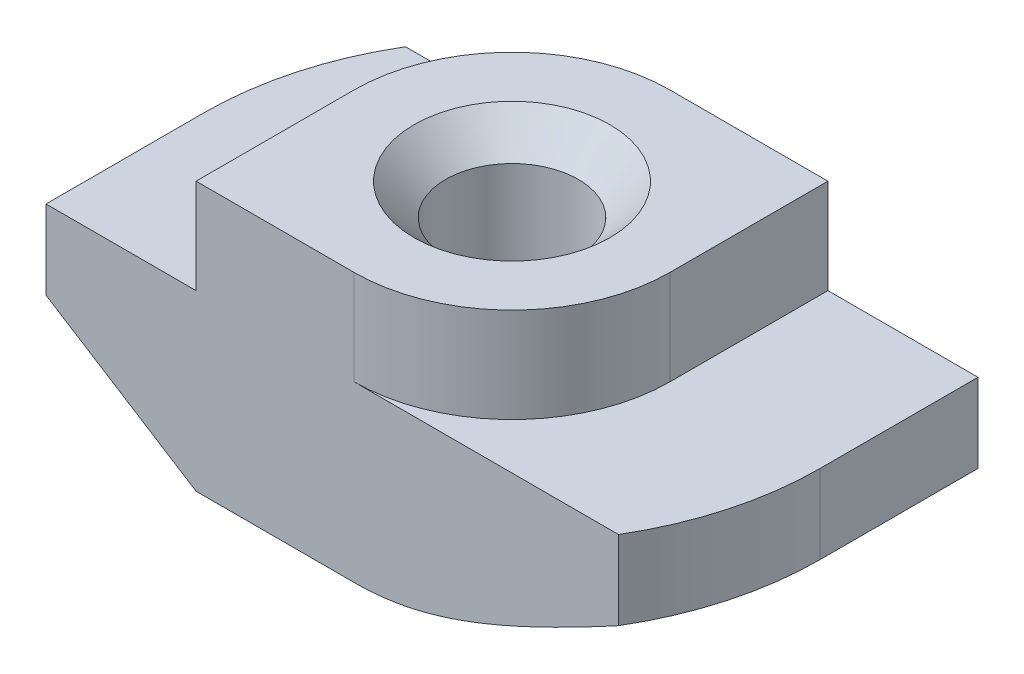
SolidWorks part; units mm, degrees
material "Сталь 20  ГОСТ 1050-2013"
ref_plane "Спереди" through (0, 0, 0) normal (0, 0, 1) x (1, 0, 0)
ref_plane "Сверху" through (0, 0, 0) normal (0, 1, 0) x (1, 0, 0)
ref_plane "Справа" through (0, 0, 0) normal (1, 0, 0) x (0, 0, -1)
sketch "Эскиз1" plane through (0, 0, 0) normal (0, 0, 1) x (1, 0, 0)
  line L0 (5, 0) -> (-5, 0)
  line L1 (-5, 0) -> (-5, -3)
  line L2 (-5, -3) -> (-9.75, -3)
  line L3 (-9.75, -3) -> (-9.75, -8.5)
  line L4 (-9.75, -8.5) -> (9.75, -8.5)
  line L5 (0, -8.5) -> (0, 0) construction
  line L6 (9.75, -3) -> (9.75, -8.5)
  line L7 (5, -3) -> (9.75, -3)
  line L8 (5, 0) -> (5, -3)
  dimension "D1" = 10
  dimension "D2" = 19.5
  dimension "D3" = 8.5
  dimension "D4" = 3
extrude "Бобышка-Вытянуть1" add sketch "Эскиз1" along normal mid plane 10
hole_wizard "Отверстие обработанное метчиком M51" positions "Эскиз2" profile "Эскиз3" tap size "M5" standard "ISO" end condition up to next
sketch "Эскиз2" plane through (0, 0, 0) normal (0, 1, 0) x (1, 0, 0)
  point P0 (0, 0)
sketch "Эскиз3" plane through (0, 0, 0) normal (1, 0, 0) x (0, 0, 1)
  line L0 (0, 0) -> (0, 8.5)
  line L1 (0, 8.5) -> (3.1, 8.5)
  line L2 (2.1, 7.5) -> (2.1, 1)
  line L3 (2.1, 1) -> (3.1, 0)
  line L5 (3.1, 0) -> (0, 0)
  line L6 (-2.1, 1) -> (-3.1, 0) construction
  line L7 (3.1, 8.5) -> (2.1, 7.5)
  line L8 (-3.1, 8.5) -> (-2.1, 7.5) construction
  line L11 (0, -6.35) -> (0, 107.95) construction
  dimension "Диаметр проходного сверла" = 4.2
  dimension "Глубина проходного сверла" = 8.5
  dimension "Диаметр передней зенковки" = 6.2
  dimension "Угол передней зенковки" = 90
  dimension "Диаметр задней зенковки" = 6.2
  dimension "Угол задней зенковки" = 90
cosmetic thread "Отверстие резьбы1" parameters "D2"=5
sketch "Эскиз4" plane through (0, 0, 0) normal (0, 1, 0) x (1, 0, 0)
  line L0 (-5, 5) -> (-5, 0)
  line L1 (-5, -5) -> (-5, 5) construction
  line L2 (5, 5) -> (-5, 5) construction
  line L3 (0, 5) -> (-5, 5)
  line L4 (0, -5) -> (5, -5)
  line L5 (5, -5) -> (-5, -5) construction
  line L6 (5, -5) -> (5, 0)
  line L7 (5, -5) -> (5, 5) construction
  arc A0 (-5, 0) -> (0, 5) centre (0, 0) cw
  arc A1 (5, 0) -> (0, -5) centre (0, 0) cw
extrude "Вырез-Вытянуть1" cut sketch "Эскиз4" against normal up to surface (3 mm away) up to face at (-7.375, -3, 0)
sketch "Эскиз5" plane through (0, -3, 0) normal (0, 1, 0) x (1, 0, 0)
  line L0 (-9.75, 0) -> (-9.75, 5)
  line L1 (-9.75, -5) -> (-9.75, 5) construction
  line L2 (-9.75, 5) -> (-8.3703, 5)
  line L3 (0, 5) -> (-9.75, 5) construction
  line L4 (9.75, 0) -> (9.75, -5)
  line L5 (9.75, -5) -> (9.75, 5) construction
  line L6 (9.75, -5) -> (8.3703, -5)
  line L7 (9.75, -5) -> (0, -5) construction
  arc A0 (-8.3703, 5) -> (-9.75, 0) centre (0, 0) ccw
  arc A2 (9.75, 0) -> (8.3703, -5) centre (0, 0) cw
extrude "Вырез-Вытянуть2" cut sketch "Эскиз5" against normal through all
sketch "Эскиз6" plane through (0, 0, 5) normal (0, 0, 1) x (1, 0, 0)
  line L0 (-9.75, -5.5) -> (-9.75, -8.5)
  line L1 (-9.75, -3) -> (-9.75, -8.5) construction
  line L2 (-9.75, -8.5) -> (-5, -8.5)
  line L3 (-9.75, -8.5) -> (8.3703, -8.5) construction
  line L4 (-5, -8.5) -> (-9.75, -5.5)
  line L5 (-5, -3) -> (-9.75, -3) construction
  line L6 (-5, 0) -> (-5, -3) construction
  dimension "D1" = 2.5
sketch "Эскиз7" plane through (0, -8.5, 0) normal (0, -1, 0) x (1, 0, 0)
  line L0 (0, 9.75) -> (-9.75, 9.75)
  line L1 (-9.75, 9.75) -> (-9.75, 0)
  line L2 (0, -9.75) -> (9.75, -9.75)
  line L3 (9.75, -9.75) -> (9.75, 0)
  arc A0 (-9.75, 0) -> (0, -9.75) centre (0, 0) ccw
  arc A1 (9.75, 0) -> (0, 9.75) centre (0, 0) ccw
sweep "Вырез-По траектории1" cut profiles "Эскиз6" path "Эскиз7"
